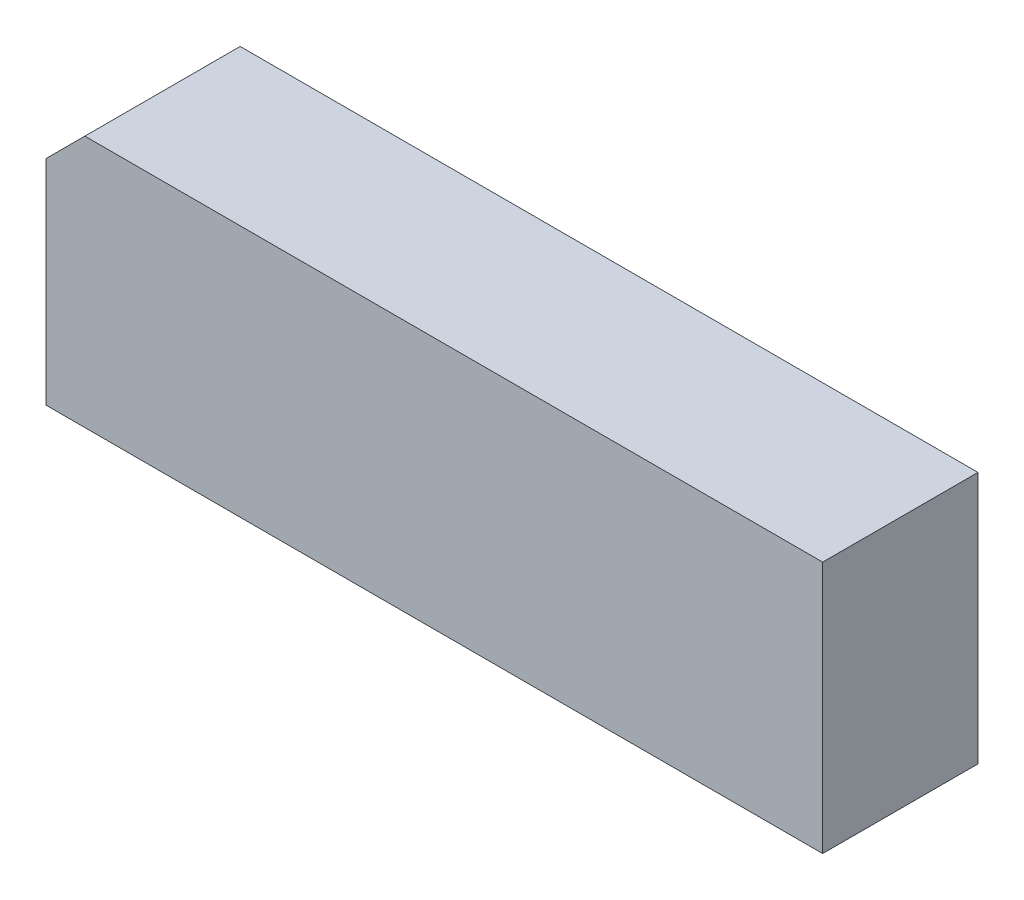
SolidWorks part; units mm, degrees
ref_plane "Ebene vorne" through (0, 0, 0) normal (0, 0, 1) x (1, 0, 0)
ref_plane "Ebene oben" through (0, 0, 0) normal (0, 1, 0) x (1, 0, 0)
ref_plane "Ebene rechts" through (0, 0, 0) normal (1, 0, 0) x (0, 0, -1)
sketch "Skizze1" plane through (0, 0, 0) normal (0, 0, 1) x (1, 0, 0)
  line L0 (0, 5.5) -> (1, 6.5)
  line L1 (0, 0) -> (20, 0)
  line L2 (0, 0) -> (0, 5.5)
  line L3 (1, 6.5) -> (20, 6.5)
  line L4 (20, 0) -> (20, 6.5)
  point P2 (0, 6.5)
  dimension "D1" = 6.5
  dimension "D2" = 20
extrude "Aufsatz-Linear austragen1" add sketch "Skizze1" along normal blind 4
